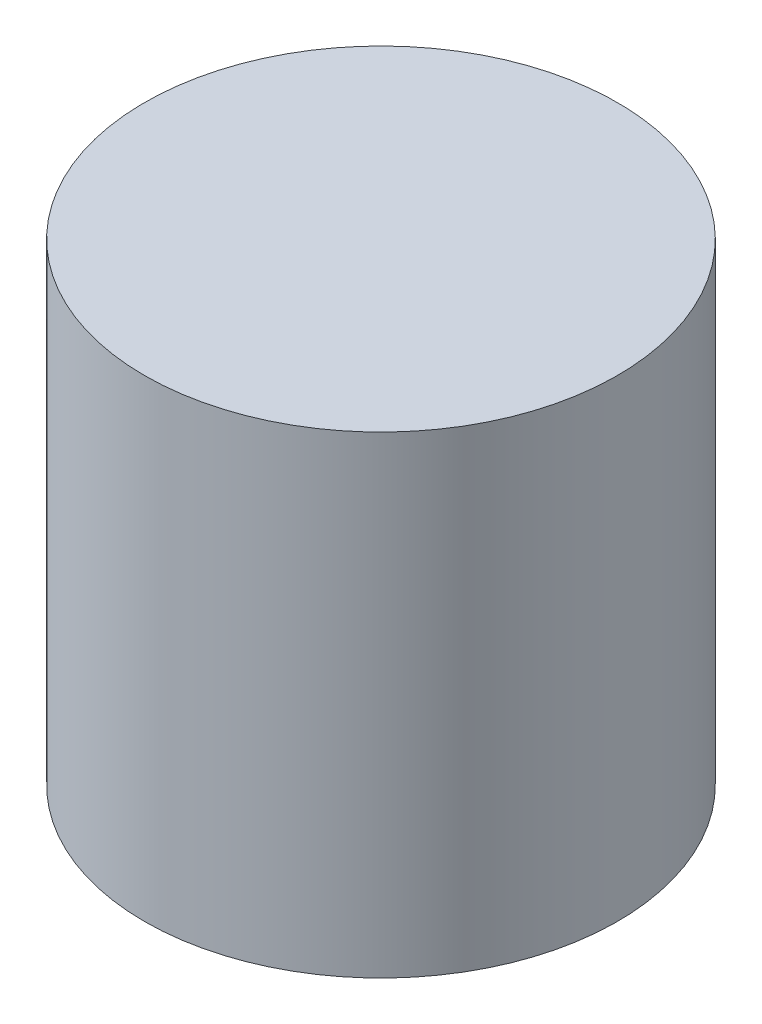
SolidWorks part; units mm, degrees
ref_plane "Front Plane" through (0, 0, 0) normal (0, 0, 1) x (1, 0, 0)
ref_plane "Top Plane" through (0, 0, 0) normal (0, 1, 0) x (1, 0, 0)
ref_plane "Right Plane" through (0, 0, 0) normal (1, 0, 0) x (0, 0, -1)
sketch "Sketch2" plane through (0, 0, 0) normal (0, 1, 0) x (1, 0, 0)
  circle A0 centre (-57.4702, 30.8636) radius 63.5
  dimension "D1" = 127
extrude "Boss-Extrude1" add sketch "Sketch2" along normal blind 127
